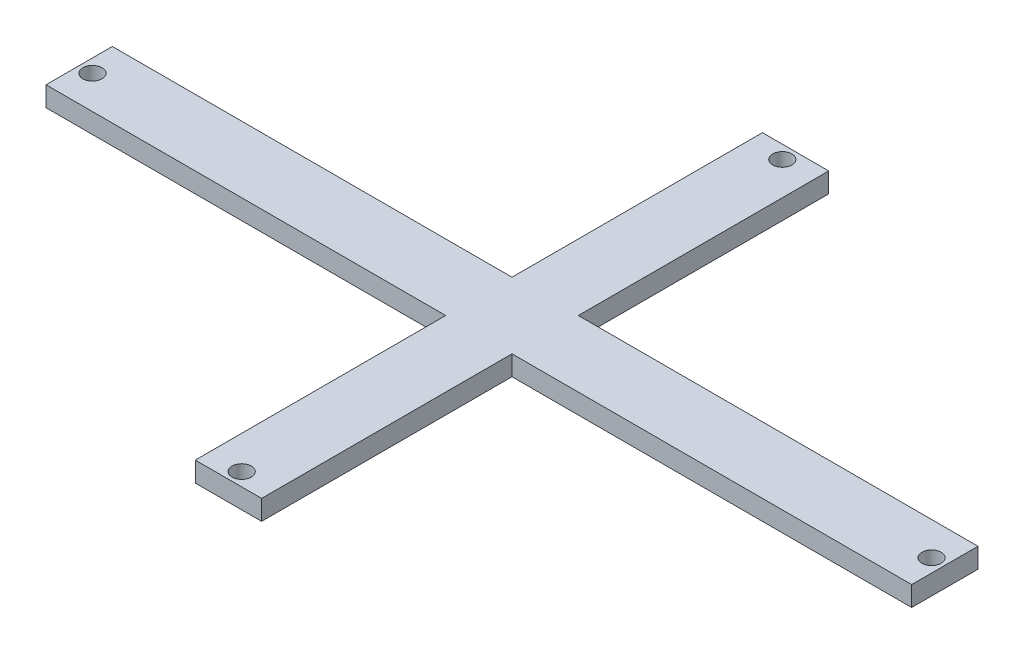
SolidWorks part; units mm, degrees
ref_plane "Front Plane" through (0, 0, 0) normal (0, 0, 1) x (1, 0, 0)
ref_plane "Top Plane" through (0, 0, 0) normal (0, 1, 0) x (1, 0, 0)
ref_plane "Right Plane" through (0, 0, 0) normal (1, 0, 0) x (0, 0, -1)
sketch "Sketch1" plane through (0, 0, 0) normal (0, 1, 0) x (1, 0, 0)
  line L1 (-25.0426, 7.6471) -> (105.4574, 7.6471)
  line L2 (-25.0426, 7.6471) -> (-25.0426, -2.3529)
  line L3 (-25.0426, -2.3529) -> (105.4574, -2.3529)
  line L4 (105.4574, 7.6471) -> (105.4574, -2.3529)
  line L5 (35.2074, 45.3971) -> (45.2074, 45.3971)
  line L6 (35.2074, 45.3971) -> (35.2074, -40.1029)
  line L7 (35.2074, -40.1029) -> (45.2074, -40.1029)
  line L8 (45.2074, 45.3971) -> (45.2074, -40.1029)
  dimension "D1" = 10
  dimension "D2" = 10
  dimension "D3" = 130.5
  dimension "D4" = 85.5
  dimension "D5" = 60.25
  dimension "D6" = 37.75
extrude "Boss-Extrude1" add sketch "Sketch1" along normal blind 3 contours L8 L1 L6 L3 | L6 L1 L2 L3 | L8 L5 L6 L1 | L8 L3 L6 L7
sketch "Sketch2" plane through (0, 3, 0) normal (0, 1, 0) x (1, 0, 0)
  line L0 (-25.0426, 7.6471) -> (35.2074, 7.6471) construction
  line L1 (-25.0426, 7.6471) -> (-25.0426, -2.3529) construction
  circle A0 centre (-23.0426, 2.6471) radius 1.25
  dimension "D1" = 2.5
  dimension "D2" = 5
  dimension "D3" = 2
sketch "Sketch6" plane through (0, 3, 0) normal (0, 1, 0) x (1, 0, 0)
  line L0 (35.2074, 45.3971) -> (45.2074, 45.3971) construction
  line L1 (45.2074, 45.3971) -> (45.2074, 7.6471) construction
  line L2 (105.4574, 7.6471) -> (105.4574, -2.3529) construction
  line L3 (45.2074, -2.3529) -> (105.4574, -2.3529) construction
  line L4 (35.2074, -40.1029) -> (45.2074, -40.1029) construction
  line L5 (35.2074, -2.3529) -> (35.2074, -40.1029) construction
  circle A0 centre (40.2074, 43.3971) radius 1.25
  circle A1 centre (103.4574, 2.6471) radius 1.25
  circle A2 centre (40.2074, -38.1029) radius 1.25
  dimension "D1" = 2.5
  dimension "D2" = 2.5
  dimension "D3" = 2.5
  dimension "D4" = 2
  dimension "D5" = 5
  dimension "D6" = 2
  dimension "D7" = 5
  dimension "D8" = 2
  dimension "D9" = 5
hole_wizard "M2.5 Clearance Hole1" positions "Sketch22" profile "Sketch23" hole size "M2.5" standard "ANSI Metric"
sketch "Sketch22" plane through (0, 3, 0) normal (0, 1, 0) x (1, 0, 0)
  point P0 (-23.0426, 2.6471)
sketch "Sketch23" plane through (-23.0426, 3, -2.6471) normal (1, 0, 0) x (0, 0, 1)
  line L0 (0, 0) -> (0, 3.8712)
  line L1 (0, 3.8712) -> (1.45, 3)
  line L2 (1.45, 3) -> (1.45, 0)
  line L5 (1.45, 0) -> (0, 0)
  line L10 (0, 3.8712) -> (-1.45, 3) construction
  line L11 (0, -6.35) -> (0, 107.95) construction
  dimension "Hole Dia." = 2.9
  dimension "Hole Depth" = 3
  dimension "Drill Angle" = 118
hole_wizard "M2.5 Clearance Hole2" positions "Sketch24" profile "Sketch25" hole size "M2.5" standard "ANSI Metric"
sketch "Sketch24" plane through (0, 3, 0) normal (0, 1, 0) x (1, 0, 0)
  point P0 (40.2074, 43.3971)
sketch "Sketch25" plane through (40.2074, 3, -43.3971) normal (1, 0, 0) x (0, 0, 1)
  line L0 (0, 0) -> (0, 3.8712)
  line L1 (0, 3.8712) -> (1.45, 3)
  line L2 (1.45, 3) -> (1.45, 0)
  line L5 (1.45, 0) -> (0, 0)
  line L10 (0, 3.8712) -> (-1.45, 3) construction
  line L11 (0, -6.35) -> (0, 107.95) construction
  dimension "Hole Dia." = 2.9
  dimension "Hole Depth" = 3
  dimension "Drill Angle" = 118
hole_wizard "M2.5 Clearance Hole3" positions "Sketch26" profile "Sketch27" hole size "M2.5" standard "ANSI Metric"
sketch "Sketch26" plane through (0, 3, 0) normal (0, 1, 0) x (1, 0, 0)
  point P0 (103.4574, 2.6471)
sketch "Sketch27" plane through (103.4574, 3, -2.6471) normal (1, 0, 0) x (0, 0, 1)
  line L0 (0, 0) -> (0, 3.8712)
  line L1 (0, 3.8712) -> (1.45, 3)
  line L2 (1.45, 3) -> (1.45, 0)
  line L5 (1.45, 0) -> (0, 0)
  line L10 (0, 3.8712) -> (-1.45, 3) construction
  line L11 (0, -6.35) -> (0, 107.95) construction
  dimension "Hole Dia." = 2.9
  dimension "Hole Depth" = 3
  dimension "Drill Angle" = 118
hole_wizard "M2.5 Clearance Hole4" positions "Sketch28" profile "Sketch29" hole size "M2.5" standard "ANSI Metric"
sketch "Sketch28" plane through (0, 3, 0) normal (0, 1, 0) x (1, 0, 0)
  point P0 (40.2074, -38.1029)
sketch "Sketch29" plane through (40.2074, 3, 38.1029) normal (1, 0, 0) x (0, 0, 1)
  line L0 (0, 0) -> (0, 3.8712)
  line L1 (0, 3.8712) -> (1.45, 3)
  line L2 (1.45, 3) -> (1.45, 0)
  line L5 (1.45, 0) -> (0, 0)
  line L10 (0, 3.8712) -> (-1.45, 3) construction
  line L11 (0, -6.35) -> (0, 107.95) construction
  dimension "Hole Dia." = 2.9
  dimension "Hole Depth" = 3
  dimension "Drill Angle" = 118
